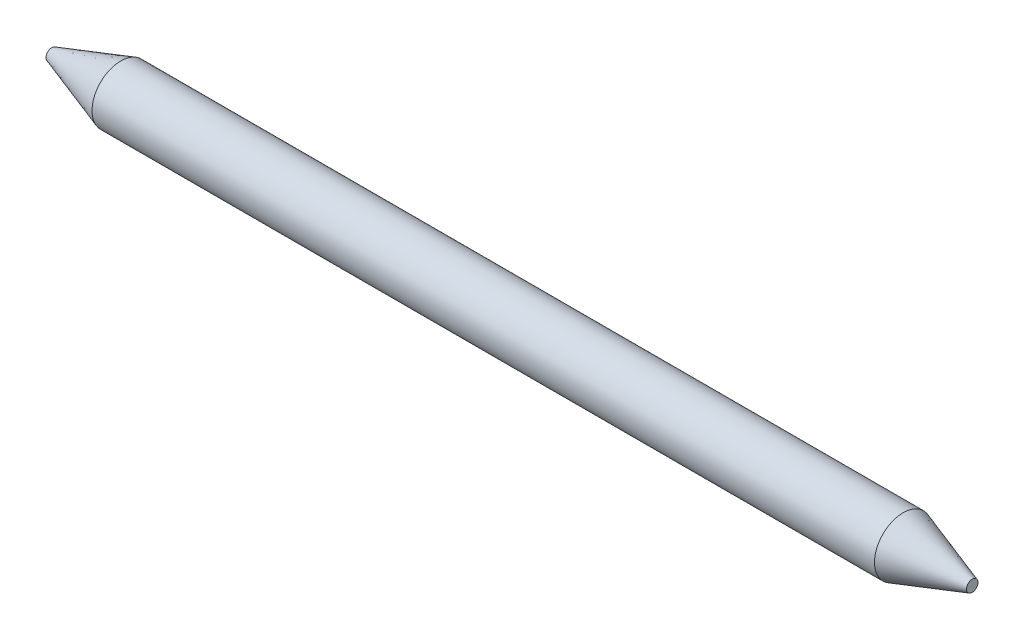
SolidWorks part; units mm, degrees
ref_plane "Front Plane" through (0, 0, 0) normal (0, 0, 1) x (1, 0, 0)
ref_plane "Top Plane" through (0, 0, 0) normal (0, 1, 0) x (1, 0, 0)
ref_plane "Right Plane" through (0, 0, 0) normal (1, 0, 0) x (0, 0, -1)
sketch "Sketch1" plane through (0, 0, 0) normal (1, 0, 0) x (0, 0, -1)
  circle A0 centre (0, 0) radius 1.5875
  dimension "D1" = 3.175
extrude "main" add sketch "Sketch1" along normal mid plane 50.8
chamfer "ends chamfer" distance 3.81 distance2 1.27 2 edges at (-25.4, 0, -1.5875) (25.4, 0, -1.5875)
